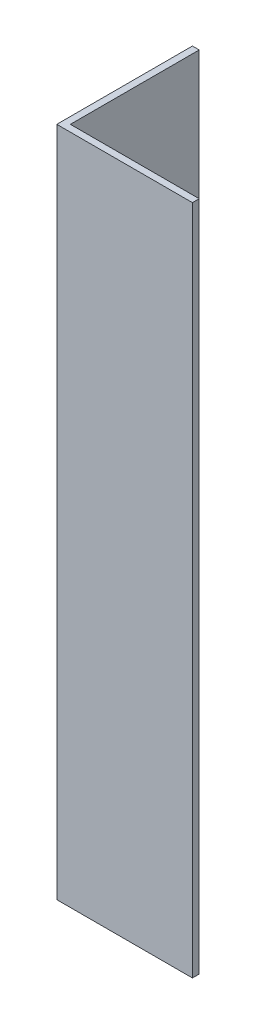
SolidWorks part; units mm, degrees
material "1060 Сплав"
ref_plane "Спереди" through (0, 0, 0) normal (0, 0, 1) x (1, 0, 0)
ref_plane "Сверху" through (0, 0, 0) normal (0, 1, 0) x (1, 0, 0)
ref_plane "Справа" through (0, 0, 0) normal (1, 0, 0) x (0, 0, -1)
sketch "Эскиз1" plane through (0, 0, 0) normal (0, 1, 0) x (1, 0, 0)
  line L0 (0, 0) -> (0, 20)
  line L1 (0, 20) -> (1, 20)
  line L2 (1, 20) -> (1, 1)
  line L3 (1, 1) -> (20, 1)
  line L4 (20, 1) -> (20, 0)
  line L5 (20, 0) -> (0, 0)
  dimension "D1" = 1
  dimension "D2" = 20
extrude "Бобышка-Вытянуть1" add sketch "Эскиз1" along normal blind 99
